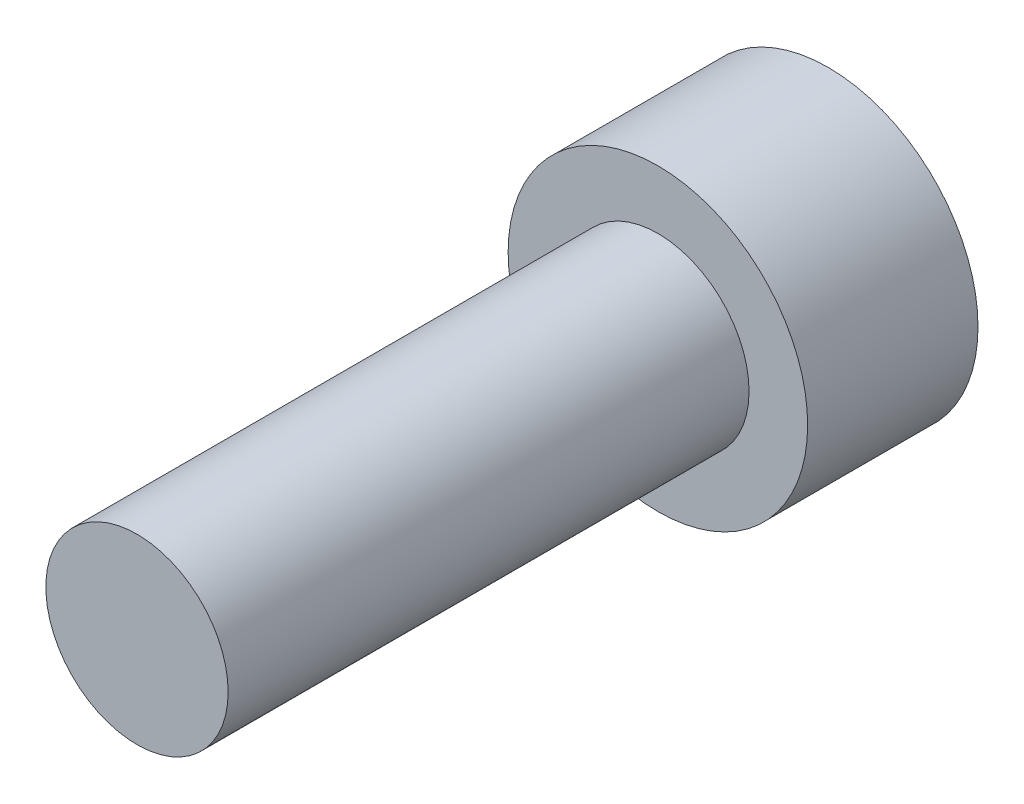
SolidWorks part; units mm, degrees
material "201 退火不锈钢 (SS)"
ref_plane "前视基准面" through (0, 0, 0) normal (0, 0, 1) x (1, 0, 0)
ref_plane "上视基准面" through (0, 0, 0) normal (0, 1, 0) x (1, 0, 0)
ref_plane "右视基准面" through (0, 0, 0) normal (1, 0, 0) x (0, 0, -1)
other "Configuration Table"
sketch "草图1" plane through (0, 0, 0) normal (0, 0, 1) x (1, 0, 0)
  circle A0 centre (0, 0) radius 2.875
  dimension "D1" = 5.75
extrude "凸台-拉伸1" add sketch "草图1" along normal blind 3.27
sketch "草图2" plane through (0, 0, 3.27) normal (0, 0, 1) x (1, 0, 0)
  circle A0 centre (0, 0) radius 1.75
  dimension "D1" = 3.5
extrude "凸台-拉伸2" add sketch "草图2" along normal blind 10
